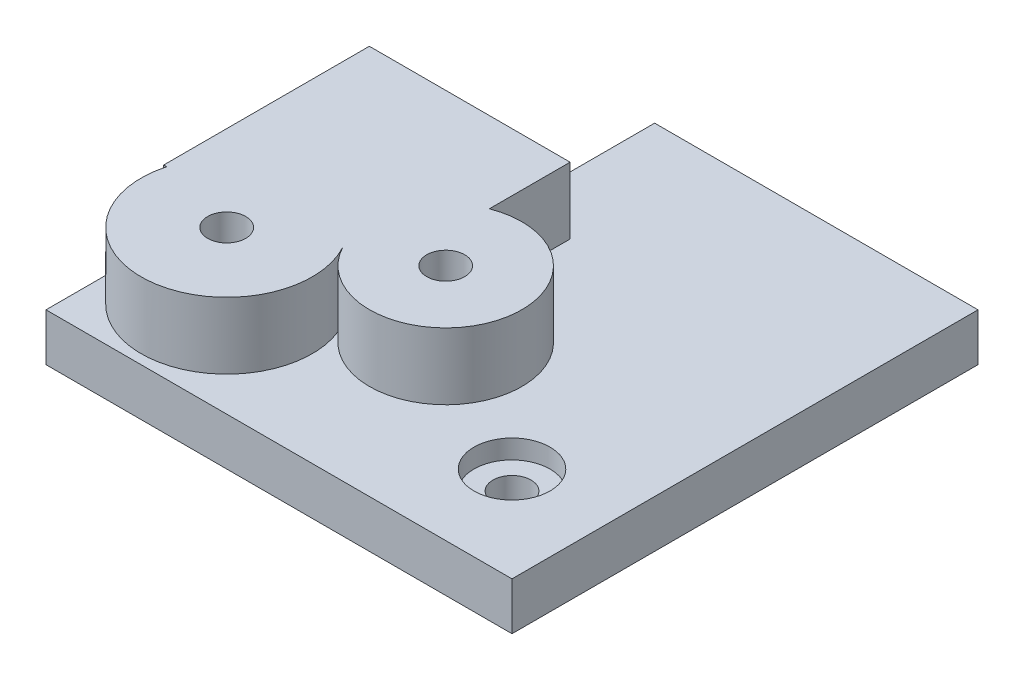
SolidWorks part; units mm, degrees
ref_plane "Front Plane" through (0, 0, 0) normal (0, 0, 1) x (1, 0, 0)
ref_plane "Top Plane" through (0, 0, 0) normal (0, 1, 0) x (1, 0, 0)
ref_plane "Right Plane" through (0, 0, 0) normal (1, 0, 0) x (0, 0, -1)
sketch "Sketch1" plane through (0, 0, 0) normal (0, 1, 0) x (1, 0, 0)
  line L1 (0, 0) -> (49, 0)
  line L2 (0, 0) -> (0, 49)
  line L3 (0, 49) -> (49, 49)
  line L4 (49, 0) -> (49, 49)
  line L5 (0, 49) -> (15, 49)
  line L6 (0, 49) -> (0, 34)
  line L7 (0, 34) -> (15, 34)
  line L8 (15, 49) -> (15, 34)
  circle A0 centre (39, 10) radius 2
  circle A1 centre (9, 10) radius 2
  circle A2 centre (24, 18.03) radius 2
  dimension "D7" = 4
  dimension "D8" = 4
  dimension "D11" = 4
  dimension "D1" = 49
  dimension "D2" = 49
  dimension "D3" = 15
  dimension "D4" = 15
  dimension "D5" = 10
  dimension "D6" = 10
  dimension "D9" = 30
  dimension "D10" = 8.03
  dimension "D12" = 15
extrude "Boss-Extrude1" add sketch "Sketch1" along normal blind 5 contours L3 L8 L7 L2 L1 L4 A2 A1 A0
sketch "Sketch2" plane through (0, 5, 0) normal (0, 1, 0) x (1, 0, 0)
  circle A0 centre (39, 10) radius 4
  dimension "D1" = 8
extrude "Cut-Extrude1" cut sketch "Sketch2" against normal blind 2
sketch "Sketch3" plane through (0, 5, 0) normal (0, 1, 0) x (1, 0, 0)
  line L1 (0, 34) -> (21.1106, 34)
  line L2 (0, 34) -> (0, 12.3735)
  line L3 (0, 12.3735) -> (21.1106, 12.3735)
  line L4 (21.1106, 34) -> (21.1106, 12.3735)
  circle A0 centre (9, 10) radius 2
  circle A1 centre (24, 18.03) radius 2
  circle A2 centre (9, 10) radius 9
  circle A3 centre (24, 18.03) radius 8.0141
  circle M2 centre (24, 18.03) radius 2
  circle M3 centre (9, 10) radius 2
  line M6 (15, 34) -> (0, 34)
  line M7 (0, 34) -> (0, 0)
extrude "Boss-Extrude2" add sketch "Sketch3" along normal blind 12 contours A3 L4 L1 L3 A2 M6 M7 | L4 A3 L3 | L3 A2 | L3 A3 L4 M2 | L3 A2 M3
sketch "Sketch4" plane through (0, 17, 0) normal (0, 1, 0) x (1, 0, 0)
  line L1 (0, 34) -> (51.5899, 34)
  line L2 (0, 34) -> (0, -11.6353)
  line L3 (0, -11.6353) -> (51.5899, -11.6353)
  line L4 (51.5899, 34) -> (51.5899, -11.6353)
extrude "Cut-Extrude2" cut sketch "Sketch4" against normal blind 5
